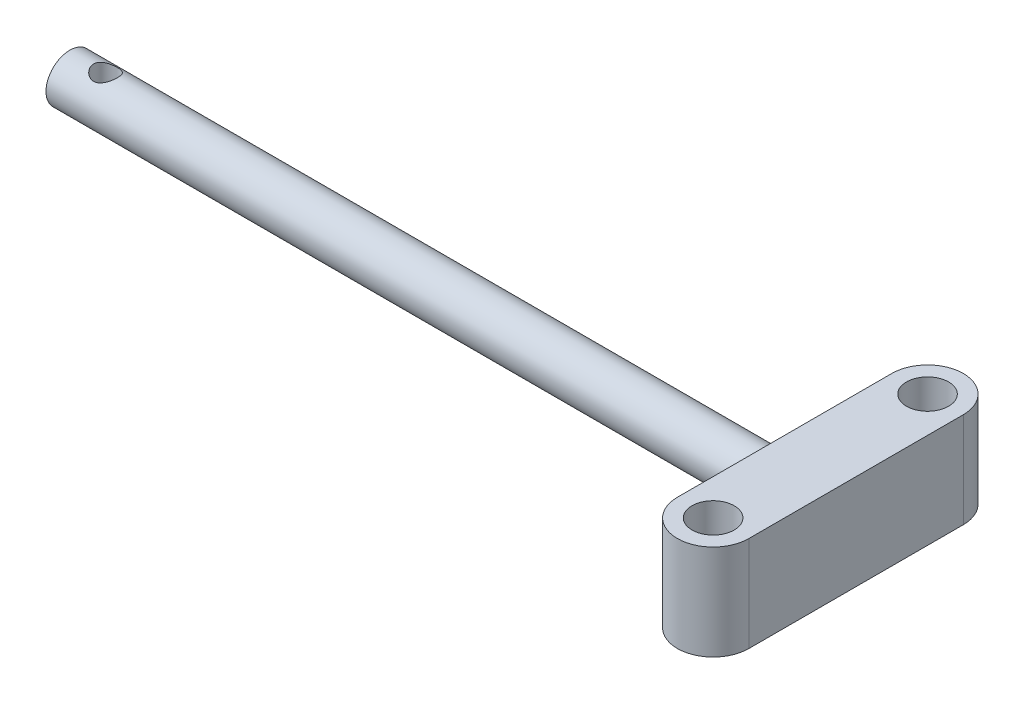
SolidWorks part; units mm, degrees
material "1.4310 (X10CrNi18-8)"
ref_plane "Front Plane" through (0, 0, 0) normal (0, 0, 1) x (1, 0, 0)
ref_plane "Top Plane" through (0, 0, 0) normal (0, 1, 0) x (1, 0, 0)
ref_plane "Right Plane" through (0, 0, 0) normal (1, 0, 0) x (0, 0, -1)
sketch "Sketch1" plane through (0, 0, 0) normal (0, 1, 0) x (1, 0, 0)
  line L0 (-65.3633, 0) -> (47.0746, 0) construction
  line L1 (0, 17.78) -> (-11.1255, 23.9048) construction
  line L2 (-11.1255, 23.9048) -> (-47.1253, 11.43) construction
  line L3 (-47.1253, 11.43) -> (-47.1253, -11.43) construction
  line L4 (-47.1253, 0) -> (-78.4896, 0) construction
  line L5 (0, -17.78) -> (-11.1255, -23.9048) construction
  line L6 (-11.1255, -23.9048) -> (-47.1253, -11.43) construction
  line L7 (0, 17.78) -> (-0.0529, 17.684) construction
  line L8 (0, -17.78) -> (-0.0529, -17.684) construction
  line L10 (-26.67, -2.7134) -> (-47.1253, -2.7134)
  line L11 (-26.67, -2.7134) -> (-26.67, 2.7134)
  line L12 (-26.67, 2.7134) -> (-47.1253, 2.7134)
  line L13 (-47.1253, -2.7134) -> (-47.1253, 2.7134)
  line L14 (-26.67, -2.7134) -> (-47.1253, 2.7134) construction
  line L15 (-26.67, 2.7134) -> (-47.1253, -2.7134) construction
  arc A0 (0, 17.78) -> (47.9287, 34.617) centre (33.3765, -0.5945) cw construction
  arc A1 (0, -17.78) -> (47.9287, -34.617) centre (33.3765, 0.5945) ccw construction
  circle A2 centre (8.89, 0) radius 6.35 construction
  circle A3 centre (15.24, 0) radius 12.7 construction
  point P3 (0, 0)
  point P25 (-36.8977, 0)
  dimension "D1" = 38.1
  dimension "D7" = 25.4
  dimension "D8" = 12.7
  dimension "D2" = 12.7
  dimension "D3" = 38.1
  dimension "D4" = 50.8
  dimension "D5" = 90
  dimension "D6" = 22.86
sketch "Sketch2" plane through (0, 0, 0) normal (0, 1, 0) x (1, 0, 0)
  line L0 (-50.9353, 2.4216) -> (-50.9353, -2.1381)
  line L16 (-50.9353, 11.43) -> (-50.9353, -11.43)
  line L17 (-50.9353, 11.43) -> (-50.9353, 2.4216)
  line L18 (-43.3153, 11.43) -> (-43.3153, -11.43)
  line L19 (-43.3153, 11.43) -> (-43.3153, -11.43)
  line L20 (-50.9353, -2.1381) -> (-50.9353, -11.43)
  arc A1 (-50.9353, -11.43) -> (-43.3153, -11.43) centre (-47.1253, -11.43) ccw
  arc A2 (-50.9353, 11.43) -> (-43.3153, 11.43) centre (-47.1253, 11.43) cw
  dimension "D3" = 3.81
  dimension "D4" = 3.81
extrude "Boss-Extrude1" add sketch "Sketch2" along normal mid plane 10.16
sketch "Sketch4" plane through (0, 5.08, 0) normal (0, 1, 0) x (1, 0, 0)
  circle A0 centre (-47.1253, 11.43) radius 2.2479
  circle A1 centre (-47.1253, -11.43) radius 2.2479
  dimension "D1" = 4.4958
extrude "Cut-Extrude1" cut sketch "Sketch4" against normal up to next
sketch "Sketch5" plane through (-50.9353, 0, 0) normal (-1, 0, 0) x (0, 0, 1)
  line L0 (-11.43, 5.08) -> (11.43, -5.08) construction
  line L1 (11.43, 5.08) -> (-11.43, -5.08) construction
  circle A0 centre (0, 0) radius 2.54
  dimension "D1" = 5.08
extrude "Boss-Extrude2" add sketch "Sketch5" along normal blind 76.2
ref_plane "Plane1" through (0, 2.54, 0) normal (0, 1, 0) x (1, 0, 0)
sketch "Sketch6" plane through (0, 2.54, 0) normal (0, 1, 0) x (1, 0, 0)
  line L0 (-88.6899, 0) -> (-43.6102, 0) construction
  line L1 (-127.1353, 2.54) -> (-127.1353, -2.54) construction
  circle A0 centre (-123.3253, 0) radius 1.27
  dimension "D1" = 2.54
  dimension "D2" = 3.81
extrude "Cut-Extrude5" cut sketch "Sketch6" against normal up to next
